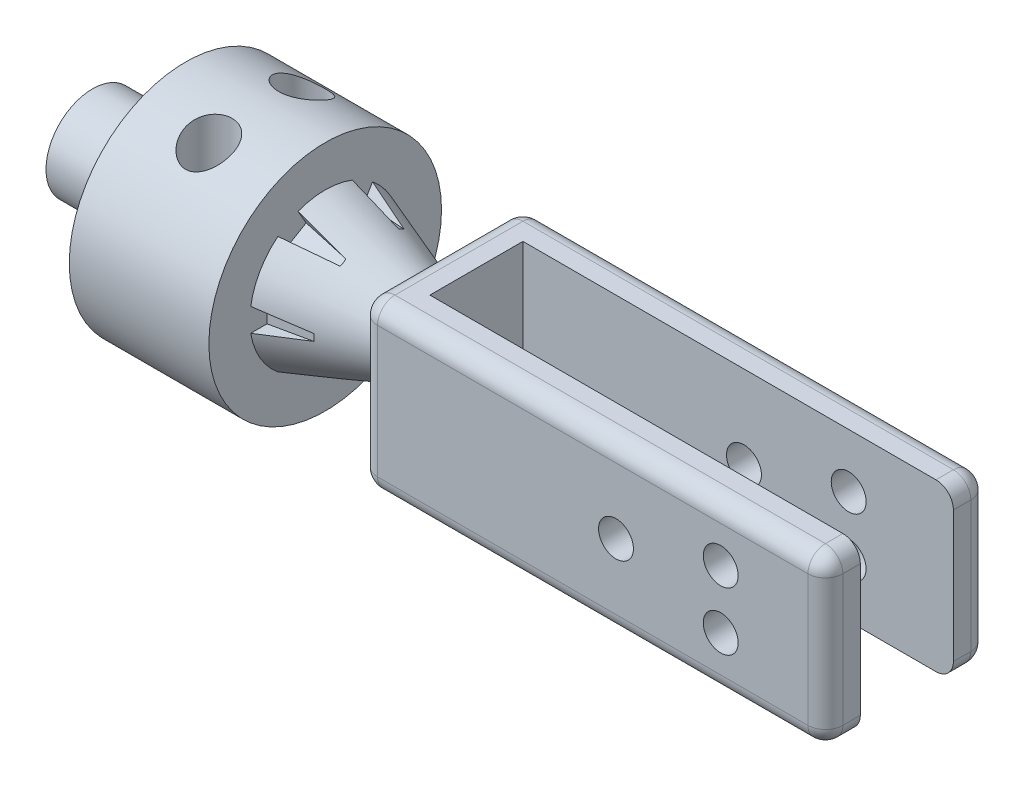
SolidWorks part; units mm, degrees
material "Chrome Stainless Steel"
ref_plane "Front Plane" through (0, 0, 0) normal (0, 0, 1) x (1, 0, 0)
ref_plane "Top Plane" through (0, 0, 0) normal (0, 1, 0) x (1, 0, 0)
ref_plane "Right Plane" through (0, 0, 0) normal (1, 0, 0) x (0, 0, -1)
sketch "Sketch1" plane through (0, 0, 0) normal (0, 0, 1) x (1, 0, 0)
  line L0 (-5657.5078, 0) -> (277217.8833, 0) construction
  line L1 (0, 0) -> (0, 40)
  line L2 (0, 40) -> (80, 40)
  line L3 (80, 40) -> (80, 100)
  line L4 (80, 100) -> (200, 100)
  line L5 (200, 100) -> (200, 64.751)
  line L6 (200, 64.751) -> (300, 28.3539)
  line L7 (300, 28.3539) -> (300, 0)
  line L8 (0, 0) -> (300, 0)
  dimension "D1" = 100
  dimension "D2" = 40
  dimension "D3" = 80
  dimension "D4" = 120
  dimension "D5" = 300
  dimension "D6" = 110
revolve "Revolve1" add sketch "Sketch1" angle 360 about L0
sketch "Sketch2" plane through (80, 0, 0) normal (-1, 0, 0) x (0, 0, 1)
  circle A0 centre (0, 0) radius 90
  dimension "D1" = 180
extrude "Cut-Extrude1" cut sketch "Sketch2" against normal blind 10
sketch "Sketch3" plane through (300, 0, 0) normal (1, 0, 0) x (0, 0, -1)
  line L1 (70, 71.4143) -> (-70, 71.4143)
  line L2 (70, 71.4143) -> (70, -71.4143)
  line L3 (70, -71.4143) -> (-70, -71.4143)
  line L4 (-70, 71.4143) -> (-70, -71.4143)
  line L5 (70, 71.4143) -> (-70, -71.4143) construction
  line L6 (70, -71.4143) -> (-70, 71.4143) construction
  circle A0 centre (0, 0) radius 100 construction
  point P0 (0, 0)
  dimension "D1" = 140
extrude "Boss-Extrude1" add sketch "Sketch3" along normal blind 400
fillet "Fillet1" radius 15 13 edges at (500, 71.4143, -70) (700, 71.4143, 0) (500, 71.4143, 70) (300, 71.4143, 0) (300, 0, 28.3539) (300, 0, 70) (300, -71.4143, 0) (300, 0, -70) (500, -71.4143, -70) (500, -71.4143, 70) (700, -71.4143, 0) (700, 0, -70) (700, 0, 70)
sketch "Sketch6" plane through (0, 0, 0) normal (0, 1, 0) x (1, 0, 0)
  circle A0 centre (140, 40) radius 20
  circle A1 centre (140, -40) radius 20
  dimension "D1" = 40
  dimension "D2" = 80
  dimension "D3" = 40
  dimension "D4" = 140
extrude "Cut-Extrude4" cut sketch "Sketch6" along normal blind 54 from offset 50
sketch "Sketch7" plane through (0, 0, 0) normal (0, 0, 1) x (1, 0, 0)
  line L0 (200, 10) -> (242.5346, 2.5)
  line L1 (200, -64.751) -> (200, 64.751) construction
  line L3 (242.5346, -2.5) -> (200, -10)
  line L4 (200, -100) -> (200, 100) construction
  line L5 (200, 10) -> (200, -10)
  arc A0 (242.5346, 2.5) -> (242.5346, -2.5) centre (240.8763, 0) cw
  dimension "D6" = 3
  dimension "D1" = 10
  dimension "D2" = 10
  dimension "D3" = 5
extrude "Cut-Extrude5" cut sketch "Sketch7" along normal blind 54 from offset 50
pattern_circular "CirPattern1" count 6 over 360 about axis through (0, 0, 0) along (1, 0, 0) of "Cut-Extrude5"
sketch "Sketch8" plane through (0, 71.4143, 0) normal (0, 1, 0) x (1, 0, 0)
  line L0 (300, 49.7762) -> (300, -49.7762) construction
  line L1 (330, 40) -> (670, 40)
  line L2 (330, 40) -> (330, -40)
  line L3 (330, -40) -> (670, -40)
  line L4 (670, 40) -> (670, -40)
  line L5 (315, 70) -> (685, 70) construction
  line L6 (700, 55) -> (700, -55) construction
  line L7 (685, -70) -> (315, -70) construction
  dimension "D1" = 30
  dimension "D2" = 30
  dimension "D3" = 30
  dimension "D4" = 30
extrude "Cut-Extrude6" cut sketch "Sketch8" against normal through all
sketch "Sketch9" plane through (0, 0, 70) normal (0, 0, 1) x (1, 0, 0)
  circle A0 centre (520, 0) radius 15
  circle A1 centre (610, 25) radius 15
  circle A2 centre (610, -25) radius 15
  dimension "D1" = 30
  dimension "D2" = 520
  dimension "D3" = 90
  dimension "D4" = 25
  dimension "D5" = 25
extrude "Cut-Extrude7" cut sketch "Sketch9" against normal through all
sketch "Sketch10" plane through (0, 0, 0) normal (0, 1, 0) x (1, 0, 0)
  line L0 (700, 55) -> (700, -55) construction
  line L1 (670, 40) -> (700, 40)
  line L2 (670, 40) -> (670, -40)
  line L3 (670, -40) -> (700, -40)
  line L4 (700, 40) -> (700, -40)
  dimension "D1" = 80
extrude "Cut-Extrude8" cut sketch "Sketch10" against normal through all both and the other way through all
